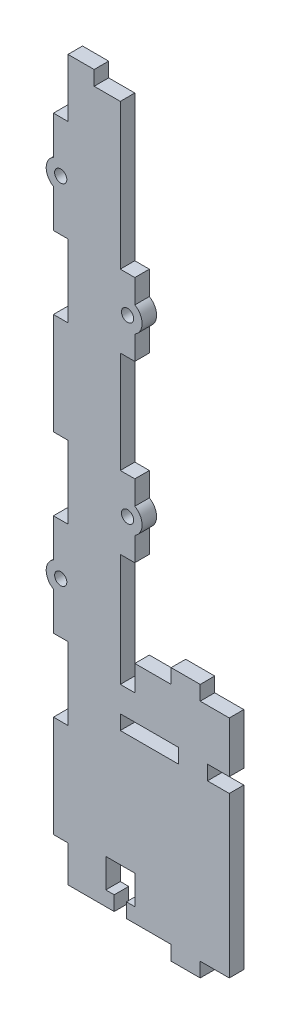
SolidWorks part; units mm, degrees
ref_plane "Front Plane" through (0, 0, 0) normal (0, 0, 1) x (1, 0, 0)
ref_plane "Top Plane" through (0, 0, 0) normal (0, 1, 0) x (1, 0, 0)
ref_plane "Right Plane" through (0, 0, 0) normal (1, 0, 0) x (0, 0, -1)
sketch "Sketch1" plane through (0, 0, 0) normal (0, 0, 1) x (1, 0, 0)
  line L1 (0, 0) -> (-18, 0)
  line L2 (0, 0) -> (0, 242.5)
  line L3 (0, 242.5) -> (-18, 242.5)
  line L4 (-18, 0) -> (-18, 242.5)
  dimension "D1" = 242.5
  dimension "D2" = 18
extrude "Boss-Extrude2" add sketch "Sketch1" along normal blind 5
sketch "Sketch2" plane through (0, 242.5, 0) normal (0, 1, 0) x (1, 0, 0)
  line L0 (0, 0) -> (-18, 0) construction
  line L1 (-18, -5) -> (-9, -5)
  line L2 (-18, -5) -> (-18, 0)
  line L3 (-18, 0) -> (-9, 0)
  line L4 (-9, -5) -> (-9, 0)
extrude "Boss-Extrude3" add sketch "Sketch2" along normal blind 5
sketch "Sketch3" plane through (0, 0, 0) normal (0, 0, -1) x (-1, 0, 0)
  line L0 (18, 247.5) -> (18, 0) construction
  line L1 (18, 227.5) -> (23, 227.5)
  line L2 (18, 227.5) -> (18, 192.5)
  line L3 (18, 192.5) -> (23, 192.5)
  line L4 (23, 227.5) -> (23, 192.5)
  line L5 (9, 247.5) -> (18, 247.5) construction
  line L6 (18, 167.5) -> (23, 167.5)
  line L7 (18, 167.5) -> (18, 132.5)
  line L8 (18, 132.5) -> (23, 132.5)
  line L9 (23, 167.5) -> (23, 132.5)
  line L10 (18, 107.5) -> (23, 107.5)
  line L11 (18, 107.5) -> (18, 72.5)
  line L12 (18, 72.5) -> (23, 72.5)
  line L13 (23, 107.5) -> (23, 72.5)
  line L15 (18, 47.5) -> (23, 47.5)
  line L16 (18, 47.5) -> (18, 12.5)
  line L17 (18, 12.5) -> (23, 12.5)
  line L18 (23, 47.5) -> (23, 12.5)
  dimension "D1" = 35
  dimension "D2" = 5
  dimension "D3" = 5
  dimension "D4" = 35
  dimension "D5" = 35
  dimension "D6" = 5
  dimension "D7" = 25
  dimension "D8" = 20
  dimension "D9" = 25
  dimension "D10" = 35
  dimension "D11" = 5
  dimension "D12" = 25
extrude "Boss-Extrude4" add sketch "Sketch3" against normal blind 5
sketch "Sketch4" plane through (0, 0, 5) normal (0, 0, 1) x (1, 0, 0)
  line L0 (0, 0) -> (0, 242.5) construction
  line L1 (0, 192.5) -> (5, 192.5)
  line L2 (0, 192.5) -> (0, 167.5)
  line L3 (0, 167.5) -> (5, 167.5)
  line L4 (5, 192.5) -> (5, 167.5)
  line L6 (-18, 192.5) -> (-23, 192.5) construction
  line L7 (-23, 167.5) -> (-18, 167.5) construction
  line L9 (0, 132.5) -> (5, 132.5)
  line L10 (0, 132.5) -> (0, 107.5)
  line L11 (0, 107.5) -> (5, 107.5)
  line L12 (5, 132.5) -> (5, 107.5)
  line L13 (-18, 132.5) -> (-23, 132.5) construction
  line L14 (-23, 107.5) -> (-18, 107.5) construction
  line L15 (-18, 72.5) -> (-23, 72.5) construction
  line L16 (0, 72.5) -> (5, 72.5) construction
  line L17 (0, 72.5) -> (0, 47.5) construction
  line L18 (0, 47.5) -> (5, 47.5) construction
  line L19 (5, 72.5) -> (5, 47.5) construction
  line L20 (-23, 47.5) -> (-18, 47.5) construction
  line L21 (-18, 12.5) -> (-23, 12.5) construction
  line L22 (0, 12.5) -> (5, 12.5) construction
  line L23 (0, 12.5) -> (0, 0) construction
  line L24 (0, 0) -> (5, 0) construction
  line L25 (5, 12.5) -> (5, 0) construction
  line L26 (-18, 0) -> (0, 0) construction
  dimension "D1" = 5
  dimension "D2" = 5
extrude "Boss-Extrude5" add sketch "Sketch4" against normal blind 5
sketch "Sketch5" plane through (0, 0, 0) normal (1, 0, 0) x (0, 0, -1)
  line L0 (0, 0) -> (0, 107.5) construction
  line L1 (-5, 0) -> (0, 0)
  line L2 (-5, 0) -> (-5, 55)
  line L3 (-5, 55) -> (0, 55)
  line L4 (0, 0) -> (0, 55)
  dimension "D1" = 55
extrude "Boss-Extrude6" add sketch "Sketch5" along normal blind 37.5
sketch "Sketch6" plane through (0, 0, 5) normal (0, 0, 1) x (1, 0, 0)
  line L0 (37.5, 55) -> (0, 55) construction
  line L1 (20, 55) -> (30, 55)
  line L2 (20, 55) -> (20, 60)
  line L3 (20, 60) -> (30, 60)
  line L4 (30, 55) -> (30, 60)
  line L5 (37.5, 55) -> (37.5, 0) construction
  dimension "D1" = 5
  dimension "D2" = 10
  dimension "D3" = 7.5
extrude "Boss-Extrude7" add sketch "Sketch6" against normal blind 5
sketch "Sketch7" plane through (0, 0, 5) normal (0, 0, 1) x (1, 0, 0)
  line L1 (0, 60) -> (5, 60)
  line L2 (0, 60) -> (0, 68.75)
  line L3 (0, 68.75) -> (5, 68.75)
  line L4 (5, 60) -> (5, 68.75)
  dimension "D1" = 8.75
extrude "Boss-Extrude8" add sketch "Sketch7" against normal blind 5
sketch "Sketch8" plane through (0, 0, 5) normal (0, 0, 1) x (1, 0, 0)
  line L0 (-18, 0) -> (37.5, 0) construction
  line L1 (17.5, 0) -> (27.5, 0)
  line L2 (17.5, 0) -> (17.5, -5)
  line L3 (17.5, -5) -> (27.5, -5)
  line L4 (27.5, 0) -> (27.5, -5)
  line L5 (37.5, 55) -> (37.5, 0) construction
  dimension "D1" = 10
  dimension "D2" = 10
  dimension "D3" = 5
extrude "Boss-Extrude9" add sketch "Sketch8" against normal blind 5
sketch "Sketch9" plane through (0, 0, 5) normal (0, 0, 1) x (1, 0, 0)
  line L1 (5, 60) -> (37.5, 60)
  line L2 (5, 60) -> (5, 77.5)
  line L3 (5, 77.5) -> (37.5, 77.5)
  line L4 (37.5, 60) -> (37.5, 77.5)
  dimension "D1" = 17.5
  dimension "D2" = 32.5
extrude "Boss-Extrude10" add sketch "Sketch9" against normal blind 5
sketch "Sketch10" plane through (0, 0, 5) normal (0, 0, 1) x (1, 0, 0)
  line L0 (37.5, 77.5) -> (5, 77.5) construction
  line L1 (17.5, 77.5) -> (27.5, 77.5)
  line L2 (17.5, 77.5) -> (17.5, 82.5)
  line L3 (17.5, 82.5) -> (27.5, 82.5)
  line L4 (27.5, 77.5) -> (27.5, 82.5)
  line L5 (37.5, 60) -> (37.5, 77.5) construction
  dimension "D1" = 5
  dimension "D2" = 10
  dimension "D3" = 10
extrude "Boss-Extrude11" add sketch "Sketch10" against normal blind 5
sketch "Sketch11" plane through (0, 0, 0) normal (0, 0, -1) x (-1, 0, 0)
  line L0 (-5, 167.5) -> (-5, 192.5) construction
  line L1 (-5, 192.5) -> (0, 192.5) construction
  line L2 (-5, 184.3301) -> (-5, 175.6699) construction
  line L3 (0, 150) -> (-19.3389, 150) construction
  line L4 (0, 132.5) -> (0, 167.5) construction
  line L5 (-5, 115.6699) -> (-5, 124.3301) construction
  circle A0 centre (-2.5, 180) radius 2.1
  arc A1 (-5, 175.6699) -> (-5, 184.3301) centre (-2.5, 180) cw construction
  arc A2 (-5, 124.3301) -> (-5, 115.6699) centre (-2.5, 120) ccw construction
  circle A3 centre (-2.5, 120) radius 2.1
  dimension "D1" = 2.5
  dimension "D2" = 4.2
  dimension "D3" = 12.5
  dimension "D4" = 5
extrude "Cut-Extrude1" cut sketch "Sketch11" against normal blind 5
sketch "Sketch12" plane through (0, 0, 0) normal (0, 0, -1) x (-1, 0, 0)
  line L0 (-5, 167.5) -> (-5, 192.5) construction
  line L1 (-5, 175.6699) -> (-5, 184.3301)
  line L2 (0, 150) -> (-22.5141, 150) construction
  line L3 (0, 132.5) -> (0, 167.5) construction
  line L4 (-5, 124.3301) -> (-5, 115.6699)
  arc A0 (-5, 184.3301) -> (-5, 175.6699) centre (-2.5, 180) ccw
  arc A1 (-5, 115.6699) -> (-5, 124.3301) centre (-2.5, 120) cw
  dimension "D1" = 5
extrude "Boss-Extrude12" add sketch "Sketch12" against normal blind 5
sketch "Sketch13" plane through (0, 0, 5) normal (0, 0, 1) x (1, 0, 0)
  line L0 (-23, 192.5) -> (-23, 227.5) construction
  line L1 (-23, 227.5) -> (-18, 227.5) construction
  line L2 (-23, 150) -> (-50.2267, 150) construction
  line L3 (-23, 132.5) -> (-23, 167.5) construction
  circle A0 centre (-20.5, 210) radius 2.1
  circle A1 centre (-20.5, 90) radius 2.1
  dimension "D1" = 4.2
  dimension "D2" = 2.5
  dimension "D3" = 17.5
extrude "Cut-Extrude2" cut sketch "Sketch13" against normal blind 5
sketch "Sketch14" plane through (0, 0, 5) normal (0, 0, 1) x (1, 0, 0)
  line L0 (-23, 192.5) -> (-23, 227.5) construction
  line L1 (-23, 214.3301) -> (-23, 205.6699)
  line L2 (-23, 150) -> (-48.0468, 150) construction
  line L3 (-23, 132.5) -> (-23, 167.5) construction
  line L4 (-23, 85.6699) -> (-23, 94.3301)
  arc A0 (-23, 205.6699) -> (-23, 214.3301) centre (-20.5, 210) cw
  arc A1 (-23, 94.3301) -> (-23, 85.6699) centre (-20.5, 90) ccw
  dimension "D1" = 5
extrude "Boss-Extrude13" add sketch "Sketch14" against normal blind 5
sketch "Sketch15" plane through (0, 0, 5) normal (0, 0, 1) x (1, 0, 0)
  line L0 (-18, 0) -> (17.5, 0) construction
  line L1 (-2.1, 0) -> (2.1, 0)
  line L2 (-2.1, 0) -> (-2.1, 5)
  line L3 (-2.1, 5) -> (2.1, 5)
  line L4 (2.1, 0) -> (2.1, 5)
  line L5 (0, 5) -> (0, 9.3346) construction
  line L6 (-5, 15) -> (5, 15)
  line L7 (-5, 15) -> (-5, 5)
  line L8 (-5, 5) -> (5, 5)
  line L9 (5, 15) -> (5, 5)
  line L10 (17.5, 0) -> (17.5, -5) construction
  point P12 (0, 15)
  dimension "D1" = 4.2
  dimension "D2" = 5
  dimension "D3" = 10
  dimension "D4" = 10
  dimension "D5" = 17.5
  dimension "D6" = 5
extrude "Cut-Extrude3" cut sketch "Sketch15" against normal blind 10
